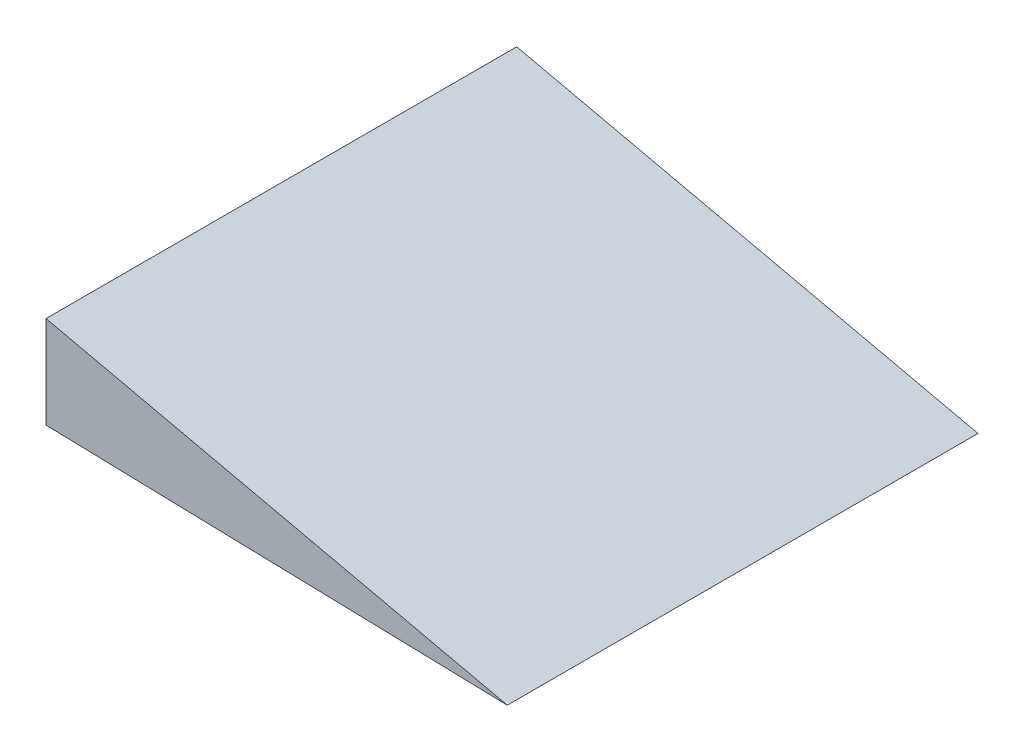
SolidWorks part; units mm, degrees
ref_plane "Plano frontal" through (0, 0, 0) normal (0, 0, 1) x (1, 0, 0)
ref_plane "Plano superior" through (0, 0, 0) normal (0, 1, 0) x (1, 0, 0)
ref_plane "Plano direito" through (0, 0, 0) normal (1, 0, 0) x (0, 0, -1)
sketch "Esboço1" plane through (0, 0, 0) normal (0, 0, 1) x (1, 0, 0)
  line L0 (-21.1323, 13.3824) -> (-21.1323, -6.6176)
  line L1 (-21.1323, -6.6176) -> (78.8344, -9.1998)
  line L2 (78.8344, -9.1998) -> (-21.1323, 13.3824)
  dimension "D1" = 20
  dimension "D2" = 100
extrude "Ressalto-extrusão1" add sketch "Esboço1" along normal blind 102
sketch "Esboço3" plane through (-0.1849, -7.1587, 0) normal (-0.0258, -0.9997, 0) x (0.9997, -0.0258, 0)
  line L0 (-20.9544, 0) -> (79.0456, 0) construction
  line L1 (-20.9544, 102) -> (79.0456, 102) construction
  line L2 (-20.9544, 102) -> (-20.9544, 0) construction
  circle A0 centre (4.0456, 25) radius 1.5
  circle A1 centre (4.0456, 77) radius 1.5
  point P10 (0, 0)
  dimension "D1" = 3
  dimension "D2" = 3
  dimension "D3" = 25
  dimension "D4" = 25
  dimension "D5" = 25
  dimension "D6" = 25
extrude "Corte-extrusão2" cut sketch "Esboço3" against normal blind 10
